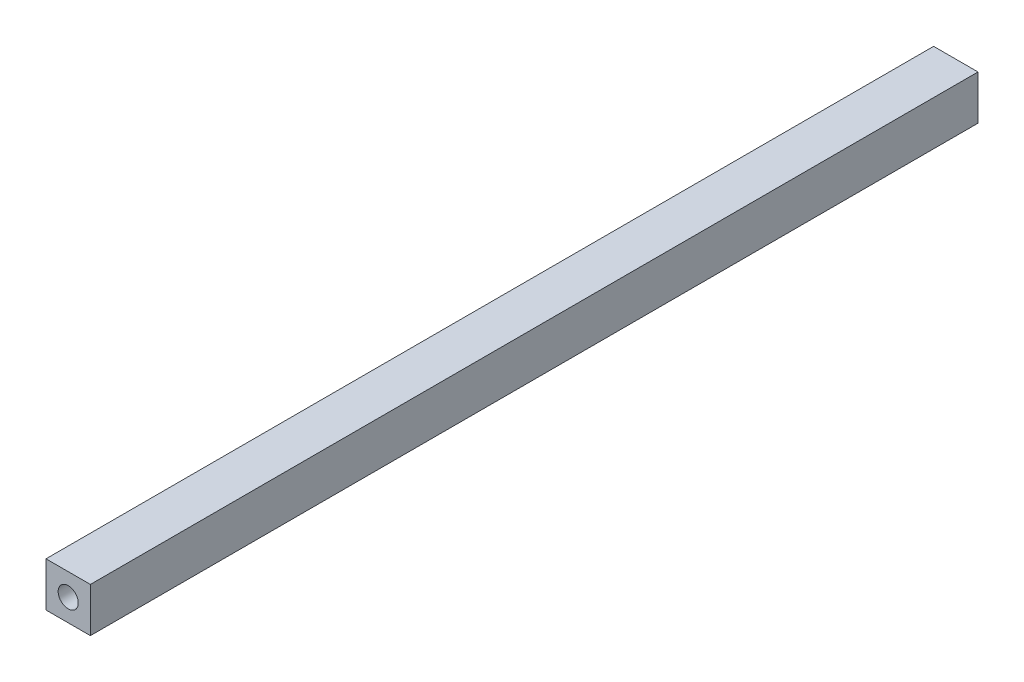
SolidWorks part; units mm, degrees
ref_plane "Front Plane" through (0, 0, 0) normal (0, 0, 1) x (1, 0, 0)
ref_plane "Top Plane" through (0, 0, 0) normal (0, 1, 0) x (1, 0, 0)
ref_plane "Right Plane" through (0, 0, 0) normal (1, 0, 0) x (0, 0, -1)
sketch "Çizim1" plane through (0, 0, 0) normal (0, 0, 1) x (1, 0, 0)
  line L1 (-7.5, 7.5) -> (7.5, 7.5)
  line L2 (-7.5, 7.5) -> (-7.5, -7.5)
  line L3 (-7.5, -7.5) -> (7.5, -7.5)
  line L4 (7.5, 7.5) -> (7.5, -7.5)
  line L5 (-7.5, 7.5) -> (7.5, -7.5) construction
  line L6 (-7.5, -7.5) -> (7.5, 7.5) construction
  point P0 (0, 0)
  dimension "D1" = 15
extrude "Yükseklik-Ekstrüzyon1" add sketch "Çizim1" along normal mid plane 300
hole_wizard "M8 Dişli Delik1" positions "Çizim2" profile "Çizim3" tap size "M8" standard "ISO"
sketch "Çizim2" plane through (0, 0, 150) normal (0, 0, 1) x (1, 0, 0)
  point P0 (0, 0)
sketch "Çizim3" plane through (0, 0, 150) normal (1, 0, 0) x (0, -1, 0)
  line L0 (0, 0) -> (0, 24.2929)
  line L1 (0, 24.2929) -> (3.4, 22.25)
  line L2 (3.4, 22.25) -> (3.4, 0)
  line L5 (3.4, 0) -> (0, 0)
  line L10 (0, 24.2929) -> (-3.4, 22.25) construction
  line L11 (0, -6.35) -> (0, 107.95) construction
  dimension "Tap Drill Dia." = 6.8
  dimension "Tap Drill Depth" = 22.25
  dimension "Drill Angle" = 118
cosmetic thread "Delik Dişi1"
mirror "Aynalama1" about plane through (0, 0, 0) normal (0, 0, 1) of "M8 Dişli Delik1"
cosmetic thread "Delik Dişi2"
